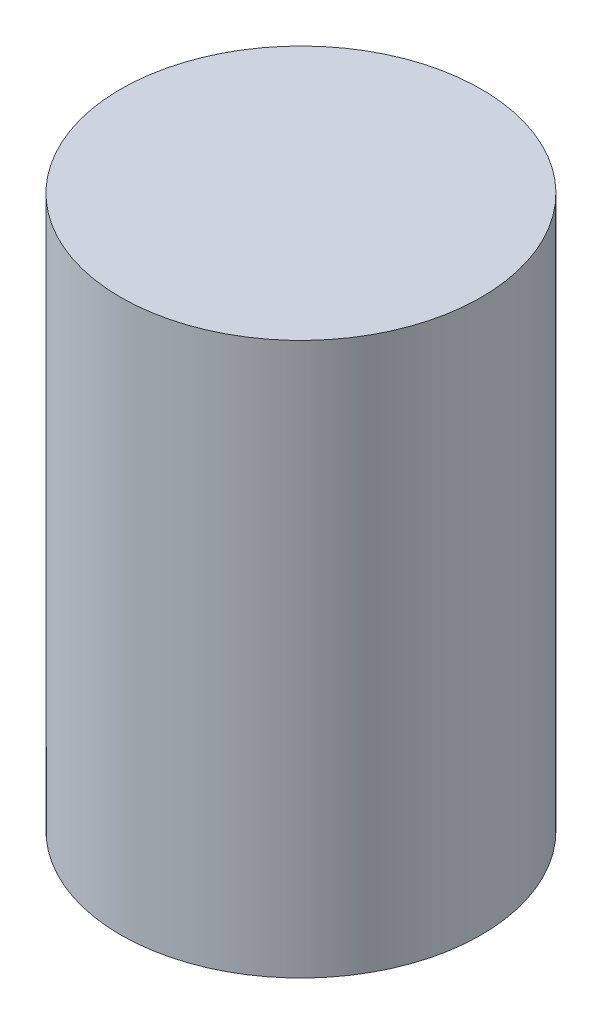
SolidWorks part; units mm, degrees
ref_plane "Front Plane" through (0, 0, 0) normal (0, 0, 1) x (1, 0, 0)
ref_plane "Top Plane" through (0, 0, 0) normal (0, 1, 0) x (1, 0, 0)
ref_plane "Right Plane" through (0, 0, 0) normal (1, 0, 0) x (0, 0, -1)
sketch "Sketch1" plane through (0, 0, 0) normal (0, 1, 0) x (1, 0, 0)
  circle A0 centre (0, 0) radius 4.064
  dimension "D1" = 8.128
extrude "Boss-Extrude1" add sketch "Sketch1" along normal blind 12.446
